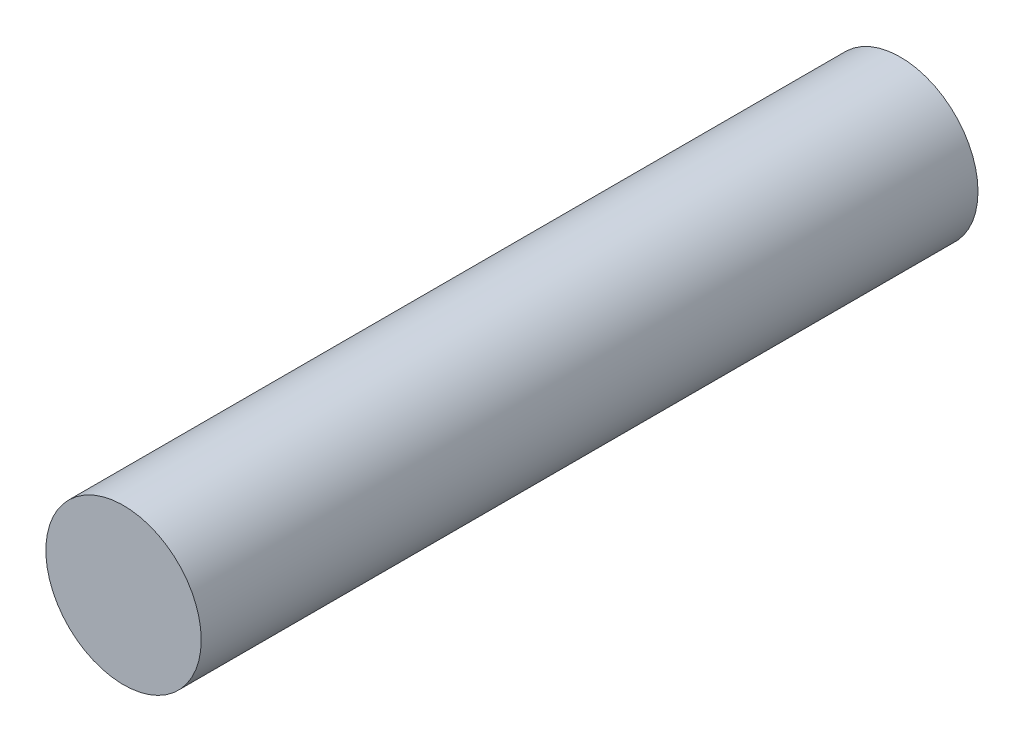
SolidWorks part; units mm, degrees
ref_plane "Front Plane" through (0, 0, 0) normal (0, 0, 1) x (1, 0, 0)
ref_plane "Top Plane" through (0, 0, 0) normal (0, 1, 0) x (1, 0, 0)
ref_plane "Right Plane" through (0, 0, 0) normal (1, 0, 0) x (0, 0, -1)
sketch "Sketch1" plane through (0, 0, 0) normal (0, 0, 1) x (1, 0, 0)
  circle A0 centre (0, 0) radius 10
  dimension "D1" = 20
extrude "Boss-Extrude1" add sketch "Sketch1" along normal blind 100
sketch "Sketch2" plane through (0, 0, 0) normal (0, 0, -1) x (-1, 0, 0)
  circle A0 centre (0, 0) radius 7.8
  dimension "D1" = 15.6
extrude "Cut-Extrude1" cut sketch "Sketch2" against normal blind 19
